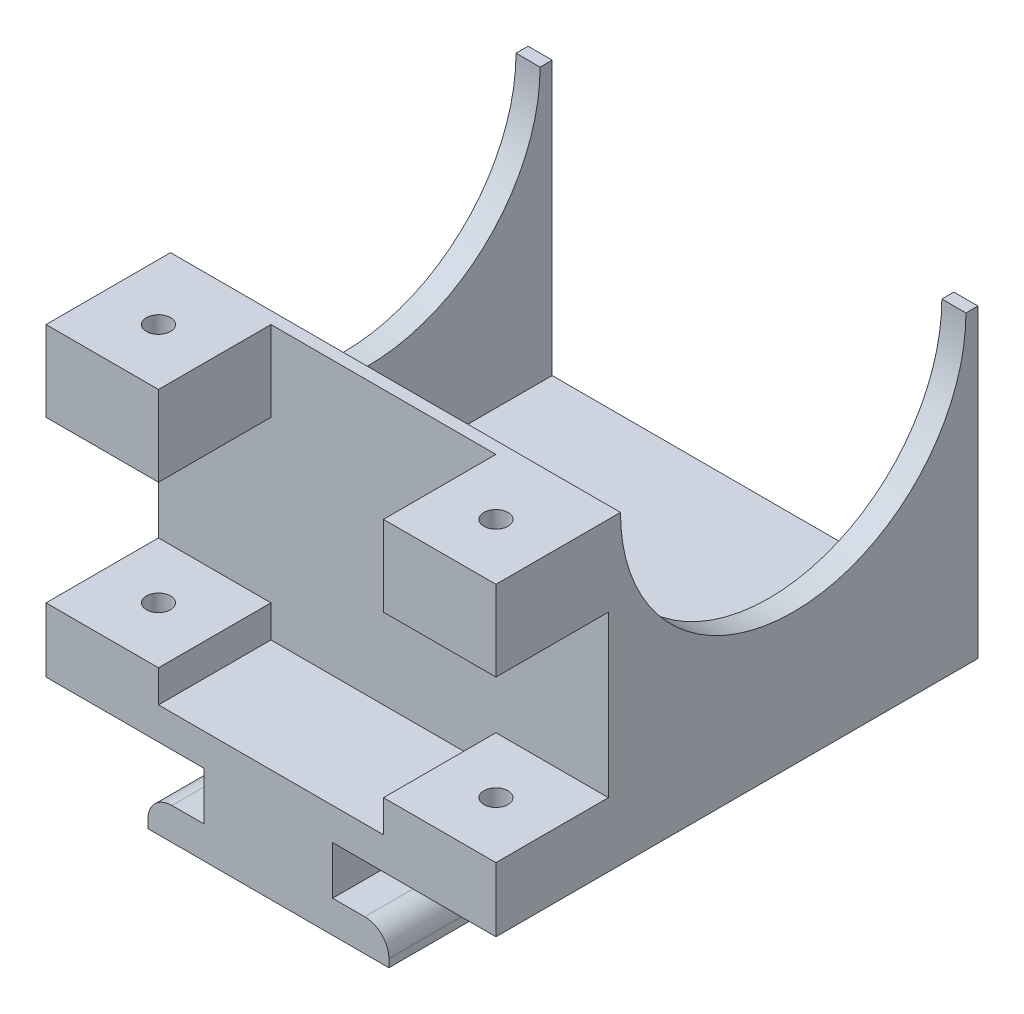
SolidWorks part; units mm, degrees
ref_plane "前视基准面" through (0, 0, 0) normal (0, 0, 1) x (1, 0, 0)
ref_plane "上视基准面" through (0, 0, 0) normal (0, 1, 0) x (1, 0, 0)
ref_plane "右视基准面" through (0, 0, 0) normal (1, 0, 0) x (0, 0, -1)
other "Configuration Table"
sketch "草图1" plane through (0, 0, 0) normal (0, 0, 1) x (1, 0, 0)
  line L0 (-13.928, -1.6693) -> (-4.0904, -1.6693)
  line L1 (-13.928, 0.3307) -> (14.072, 0.3307)
  line L2 (-13.928, 0.3307) -> (-13.928, -1.6693)
  line L3 (-7.5904, -6.6693) -> (7.4096, -6.6693)
  line L4 (14.072, 0.3307) -> (14.072, -1.6693)
  line L5 (3.9096, -1.6693) -> (14.072, -1.6693)
  line L7 (-4.0904, -1.6693) -> (-4.0904, -4.6693)
  line L9 (3.9096, -1.6693) -> (3.9096, -4.6693)
  line L10 (-4.0904, -4.6693) -> (-7.5904, -4.6693)
  line L11 (7.4096, -4.6693) -> (3.9096, -4.6693)
  line L12 (7.4096, -4.6693) -> (7.4096, -6.6693)
  line L14 (-7.5904, -4.6693) -> (-7.5904, -6.6693)
  dimension "D1" = 28
  dimension "D2" = 2
  dimension "D3" = 8
  dimension "D4" = 3
  dimension "D5" = 2
  dimension "D6" = 15
extrude "凸台-拉伸1" add sketch "草图1" along normal blind 30
fillet "圆角1" radius 1.5 2 edges at (-7.5904, -4.6693, 15) (7.4096, -4.6693, 15)
sketch "草图2" plane through (0, 0.3307, 0) normal (0, 1, 0) x (1, 0, 0)
  line L0 (0.072, 0) -> (0.072, -30) construction
  line L1 (-13.928, 0) -> (-12.428, 0)
  line L2 (-13.928, 0) -> (-13.928, -21)
  line L4 (-12.428, 0) -> (-12.428, -21)
  line L5 (14.072, 0) -> (-13.928, 0) construction
  line L6 (14.072, -30) -> (-13.928, -30) construction
  line L8 (12.572, 0) -> (12.572, -21)
  line L9 (14.072, 0) -> (12.572, 0)
  line L10 (14.072, 0) -> (14.072, -21)
  line L11 (14.072, -30) -> (14.072, 0) construction
  line L12 (-12.428, -21) -> (12.572, -21)
  line L13 (-13.928, -21) -> (-13.928, -23)
  line L14 (-13.928, -23) -> (14.072, -23)
  line L15 (14.072, -21) -> (14.072, -23)
  dimension "D1" = 1.5
  dimension "D2" = 21
  dimension "D3" = 2
  dimension "D4" = 2
extrude "凸台-拉伸3" add sketch "草图2" along normal blind 17
sketch "草图5" plane through (-13.928, 0, 0) normal (-1, 0, 0) x (0, 0, 1)
  line L0 (0, 17.3307) -> (23, 17.3307) construction
  circle A0 centre (11.5, 17.3307) radius 10.75
  dimension "D1" = 21.5
extrude "切除-拉伸2" cut sketch "草图5" against normal through all
sketch "草图6" plane through (0, 0.3307, 0) normal (0, 1, 0) x (1, 0, 0)
  line L0 (14.072, -30) -> (-13.928, -30) construction
  line L1 (-13.928, -23) -> (-6.928, -23)
  line L2 (-13.928, -23) -> (-13.928, -30)
  line L3 (-13.928, -30) -> (-6.928, -30)
  line L4 (-6.928, -23) -> (-6.928, -30)
  line L5 (-13.928, -23) -> (-6.928, -30) construction
  line L6 (0.072, -23) -> (0.072, -30) construction
  line L7 (-13.928, -23) -> (14.072, -23) construction
  line L8 (14.072, -30) -> (7.072, -30)
  line L9 (7.072, -23) -> (7.072, -30)
  line L10 (14.072, -23) -> (7.072, -23)
  line L11 (14.072, -23) -> (14.072, -30)
  circle A0 centre (-10.428, -26.5) radius 0.75
  circle A1 centre (10.572, -26.5) radius 0.75
  dimension "D2" = 1.5
  dimension "D1" = 7
extrude "凸台-拉伸4" add sketch "草图6" along normal blind 2
sketch "草图8" plane through (0, 2.3307, 0) normal (0, 1, 0) x (1, 0, 0)
  line L1 (-13.928, -23) -> (-6.928, -23)
  line L2 (-13.928, -23) -> (-13.928, -30)
  line L3 (-13.928, -30) -> (-6.928, -30)
  line L4 (-6.928, -23) -> (-6.928, -30)
  line L5 (7.072, -23) -> (14.072, -23)
  line L6 (7.072, -23) -> (7.072, -30)
  line L7 (7.072, -30) -> (14.072, -30)
  line L8 (14.072, -23) -> (14.072, -30)
  circle A0 centre (10.572, -26.5) radius 0.75
  circle A1 centre (-10.428, -26.5) radius 0.75
  dimension "D1" = 1.5
  dimension "D2" = 1.5
extrude "凸台-拉伸5" add sketch "草图8" against normal blind 5 from surface at 15 starting at face at (-13.178, 17.3307, 0.375)
